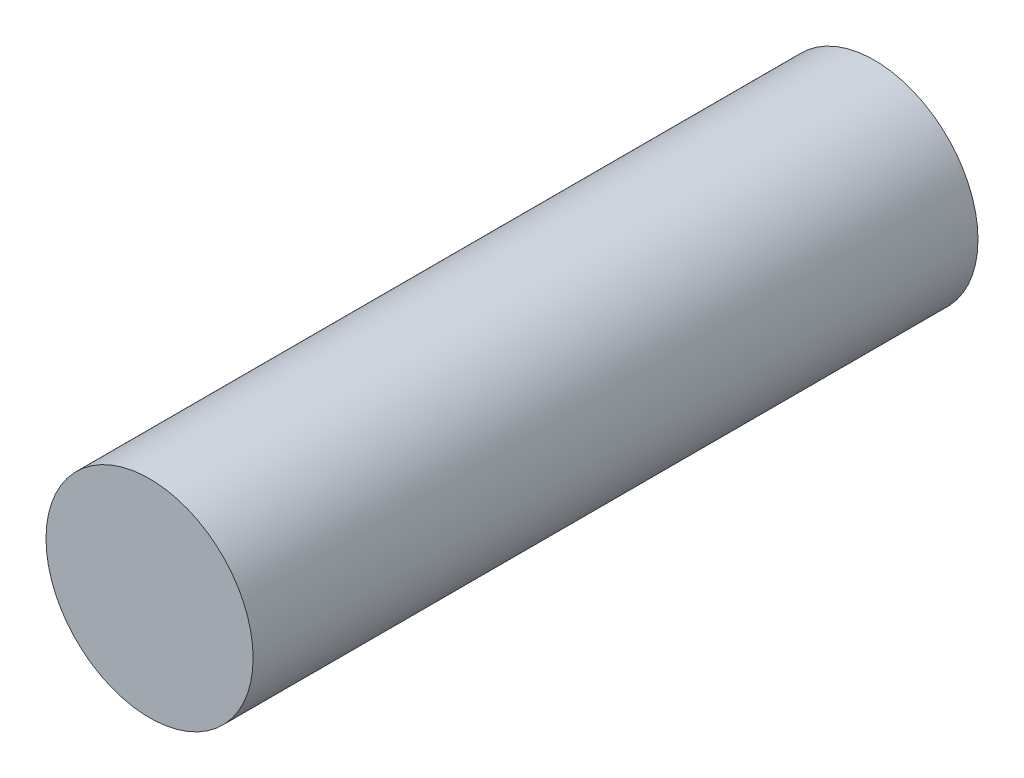
SolidWorks part; units mm, degrees
ref_plane "Plan de face" through (0, 0, 0) normal (0, 0, 1) x (1, 0, 0)
ref_plane "Plan de dessus" through (0, 0, 0) normal (0, 1, 0) x (1, 0, 0)
ref_plane "Plan de droite" through (0, 0, 0) normal (1, 0, 0) x (0, 0, -1)
sketch "Esquisse1" plane through (0, 0, 0) normal (0, 0, 1) x (1, 0, 0)
  circle A0 centre (-383.125, -140.1613) radius 4
  dimension "D1" = 8
extrude "Boss.-Extru.1" add sketch "Esquisse1" against normal blind 28
